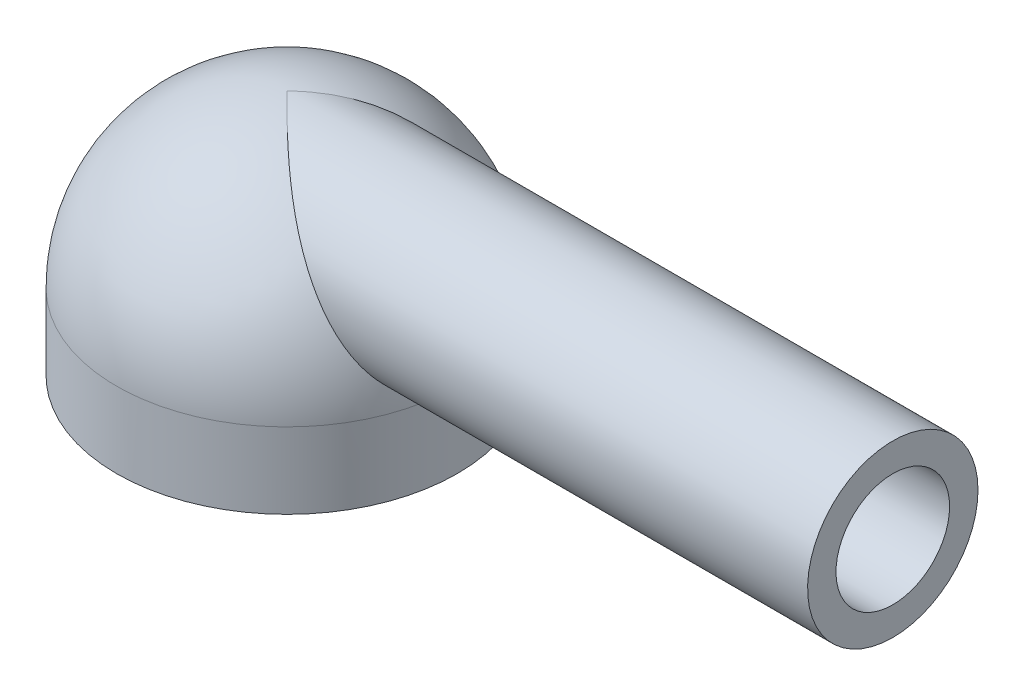
SolidWorks part; units mm, degrees
ref_plane "前视基准面" through (0, 0, 0) normal (0, 0, 1) x (1, 0, 0)
ref_plane "上视基准面" through (0, 0, 0) normal (0, 1, 0) x (1, 0, 0)
ref_plane "右视基准面" through (0, 0, 0) normal (1, 0, 0) x (0, 0, -1)
other "Configuration Table"
sketch "草图1" plane through (0, 0, 0) normal (0, 1, 0) x (1, 0, 0)
  circle A0 centre (0, 0) radius 1.75
  circle A1 centre (0, 0) radius 2.25
extrude "凸台-拉伸1" add sketch "草图1" along normal blind 1
sketch "草图2" plane through (0, 0, 0) normal (1, 0, 0) x (0, 0, -1)
  line L0 (0, 0) -> (0, 1)
  line L1 (0, 1) -> (0, 3.25)
  line L2 (0, 1) -> (-2.25, 1)
  arc A0 (0, 3.25) -> (-2.25, 1) centre (0, 1) ccw
ref_axis "基准轴1" through (0, 0, 0) along (0, 1, 0)
revolve "旋转1" add sketch "草图2" angle 360 about axis through (0, 0, 0) along (0, 1, 0)
sketch "草图3" plane through (0, 0, 0) normal (1, 0, 0) x (0, 0, -1)
  line L0 (0, 1) -> (0, 3.25)
  line L1 (-2.25, 1) -> (2.25, 1) construction
  arc A0 (2.25, 1) -> (-2.25, 1) centre (0, 1) ccw construction
  circle A1 centre (0, 2.125) radius 1.125
  circle A2 centre (0, 2.125) radius 0.75
extrude "凸台-拉伸2" add sketch "草图3" along normal blind 8 contours L0 A1 | L0 A1
